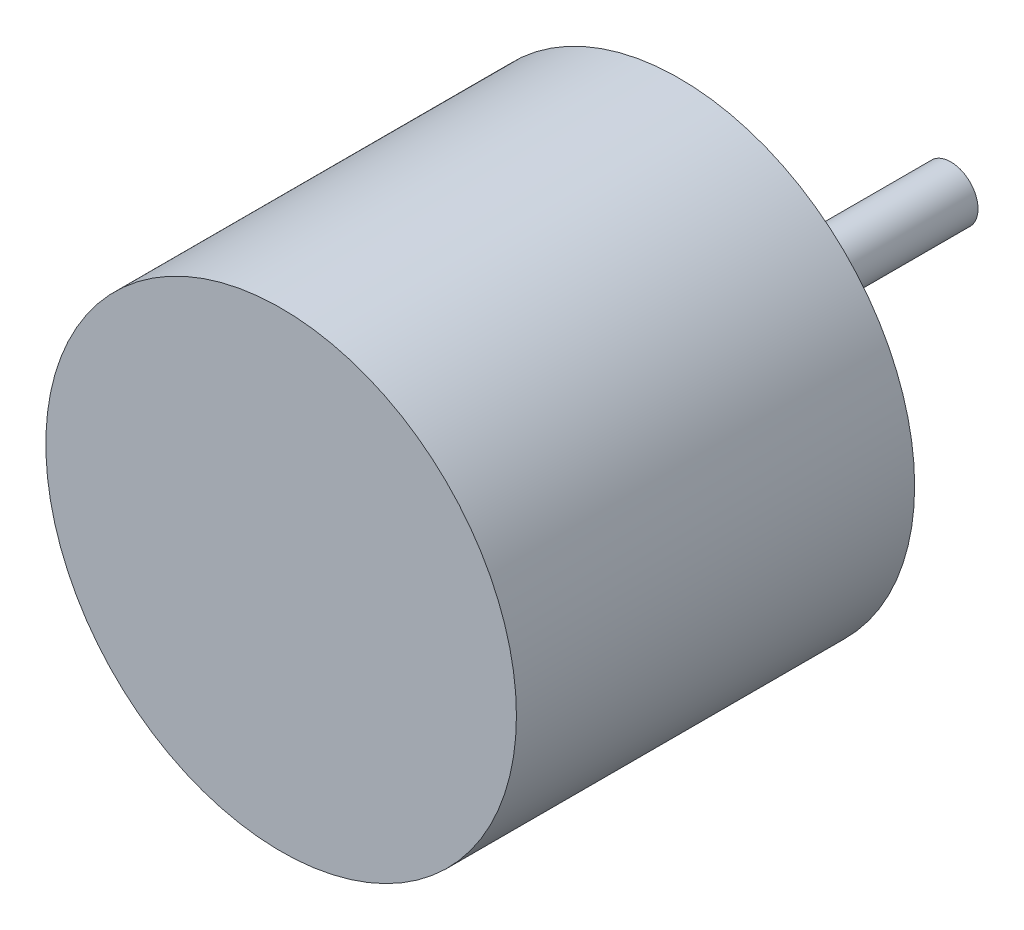
SolidWorks part; units mm, degrees
ref_plane "Plan de face" through (0, 0, 0) normal (0, 0, 1) x (1, 0, 0)
ref_plane "Plan de dessus" through (0, 0, 0) normal (0, 1, 0) x (1, 0, 0)
ref_plane "Plan de droite" through (0, 0, 0) normal (1, 0, 0) x (0, 0, -1)
sketch "Esquisse1" plane through (0, 0, 0) normal (0, 0, 1) x (1, 0, 0)
  circle A0 centre (0, 0) radius 13
  dimension "D1" = 26
extrude "Boss.-Extru.1" add sketch "Esquisse1" along normal blind 22
sketch "Esquisse2" plane through (0, 0, 0) normal (0, 0, -1) x (-1, 0, 0)
  circle A0 centre (0, 0) radius 1.5
  dimension "D1" = 3
extrude "Boss.-Extru.2" add sketch "Esquisse2" along normal blind 15
